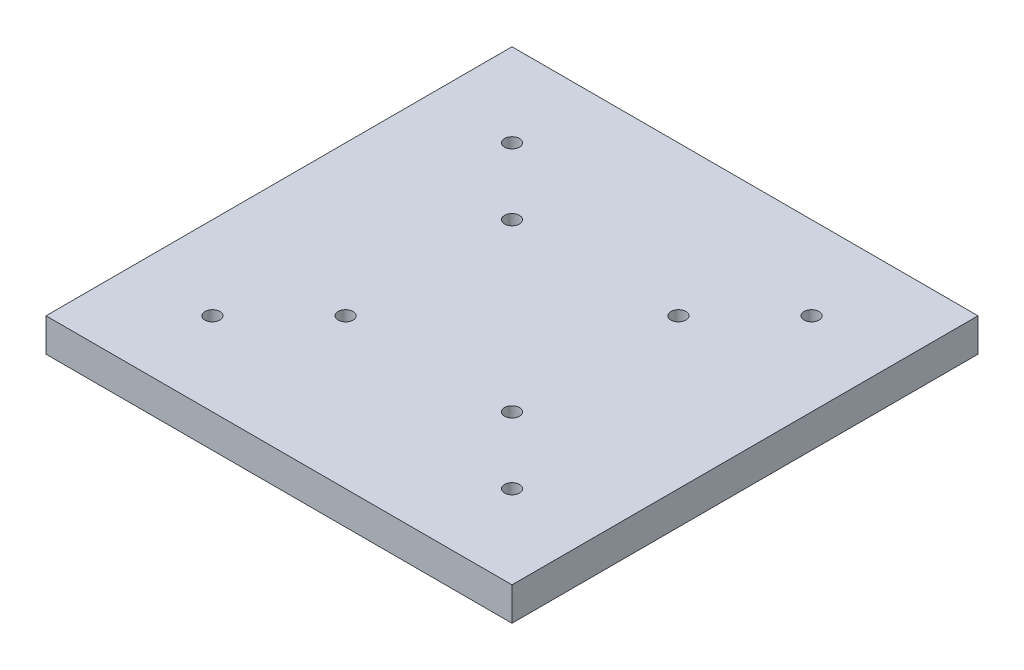
SolidWorks part; units mm, degrees
ref_plane "Front Plane" through (0, 0, 0) normal (0, 0, 1) x (1, 0, 0)
ref_plane "Top Plane" through (0, 0, 0) normal (0, 1, 0) x (1, 0, 0)
ref_plane "Right Plane" through (0, 0, 0) normal (1, 0, 0) x (0, 0, -1)
sketch "Sketch1" plane through (0, 0, 0) normal (0, 1, 0) x (1, 0, 0)
  line L1 (-25, -25) -> (25, -25) construction
  line L2 (-25, -25) -> (-25, 25) construction
  line L3 (-25, 25) -> (25, 25) construction
  line L4 (25, -25) -> (25, 25) construction
  line L5 (-25, -25) -> (25, 25) construction
  line L6 (-25, 25) -> (25, -25) construction
  line L7 (45, 45) -> (-45, 45) construction
  line L8 (45, 45) -> (45, -45) construction
  line L9 (45, -45) -> (-45, -45) construction
  line L10 (-45, 45) -> (-45, -45) construction
  line L11 (45, 45) -> (-45, -45) construction
  line L12 (45, -45) -> (-45, 45) construction
  line L13 (70, 70) -> (-70, 70)
  line L14 (70, 70) -> (70, -70)
  line L15 (70, -70) -> (-70, -70)
  line L16 (-70, 70) -> (-70, -70)
  line L17 (70, 70) -> (-70, -70) construction
  line L18 (70, -70) -> (-70, 70) construction
  point P0 (0, 0)
  point P6 (0, 0)
  point P11 (0, 0)
  dimension "D1" = 50
  dimension "D2" = 90
  dimension "D3" = 140
extrude "Boss-Extrude1" add sketch "Sketch1" against normal blind 10
hole_wizard "M4 Clearance Hole1" positions "Sketch2" profile "Sketch4" hole size "M4" standard "ANSI Metric" end condition through all
sketch "Sketch2" plane through (0, 0, 0) normal (0, 1, 0) x (1, 0, 0)
  point P0 (-45, 45)
  point P3 (-45, -45)
  point P6 (45, -45)
  point P9 (45, 45)
  point P12 (25, 25)
  point P15 (-25, 25)
  point P18 (-25, -25)
  point P21 (25, -25)
sketch "Sketch4" plane through (-45, 0, -45) normal (1, 0, 0) x (0, 0, 1)
  line L0 (0, 0) -> (0, 10)
  line L1 (0, 10) -> (2.25, 10)
  line L2 (2.25, 10) -> (2.25, 0)
  line L5 (2.25, 0) -> (0, 0)
  line L11 (0, -6.35) -> (0, 107.95) construction
  dimension "Thru Hole Dia." = 4.5
  dimension "Thru Hole Depth" = 10
